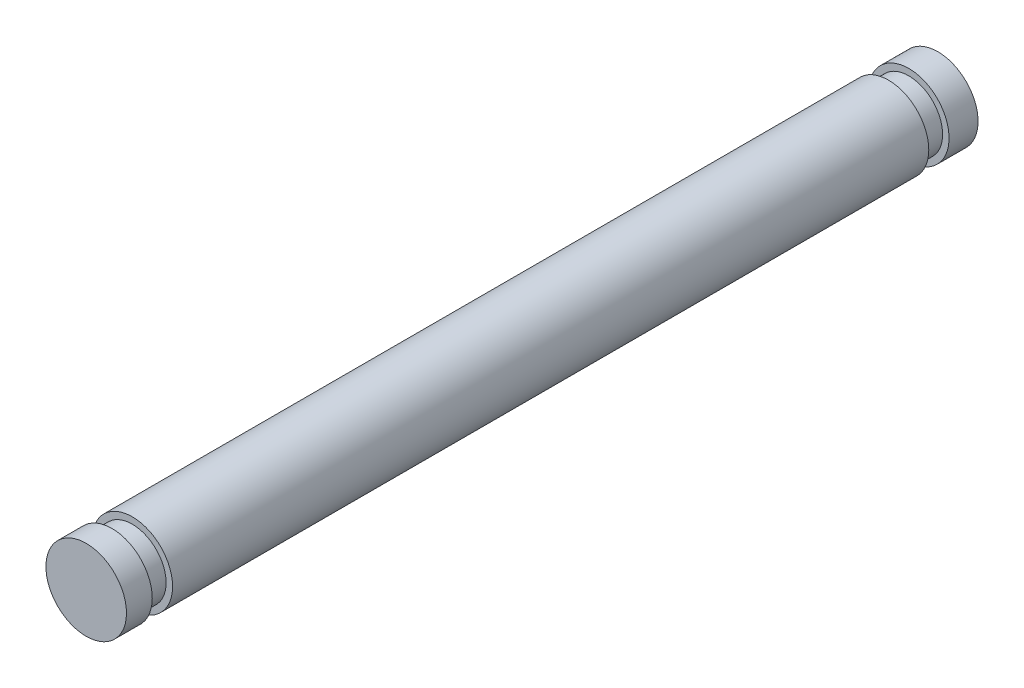
SolidWorks part; units mm, degrees
ref_plane "Front Plane" through (0, 0, 0) normal (0, 0, 1) x (1, 0, 0)
ref_plane "Top Plane" through (0, 0, 0) normal (0, 1, 0) x (1, 0, 0)
ref_plane "Right Plane" through (0, 0, 0) normal (1, 0, 0) x (0, 0, -1)
sketch "Sketch1" plane through (0, 0, 0) normal (0, 0, 1) x (1, 0, 0)
  circle A0 centre (0, 0) radius 3.175
  dimension "D1" = 6.35
extrude "Boss-Extrude1" add sketch "Sketch1" along normal blind 59.6138
sketch "Sketch2" plane through (0, 0, 0) normal (0, 0, -1) x (-1, 0, 0)
  circle A0 centre (0, 0) radius 2.667
  dimension "D1" = 5.334
extrude "Boss-Extrude2" add sketch "Sketch2" along normal blind 1.6002
sketch "Sketch3" plane through (0, 0, -1.6002) normal (0, 0, -1) x (-1, 0, 0)
  circle A0 centre (0, 0) radius 3.175
extrude "Boss-Extrude3" add sketch "Sketch3" along normal blind 2.286
sketch "Sketch4" plane through (0, 0, 59.6138) normal (0, 0, 1) x (1, 0, 0)
  circle A0 centre (0, 0) radius 2.667
  dimension "D1" = 5.334
extrude "Boss-Extrude4" add sketch "Sketch4" along normal blind 1.6002
sketch "Sketch5" plane through (0, 0, 61.214) normal (0, 0, 1) x (1, 0, 0)
  circle A0 centre (0, 0) radius 3.175
  dimension "D1" = 6.35
extrude "Boss-Extrude5" add sketch "Sketch5" along normal blind 2.032
